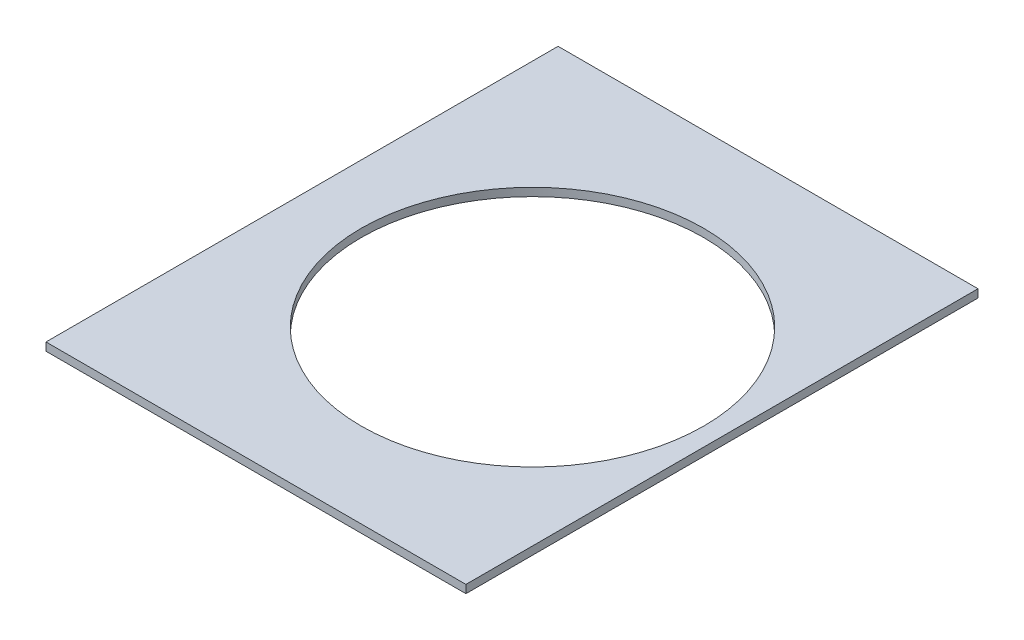
SolidWorks part; units mm, degrees
ref_plane "Front Plane" through (0, 0, 0) normal (0, 0, 1) x (1, 0, 0)
ref_plane "Top Plane" through (0, 0, 0) normal (0, 1, 0) x (1, 0, 0)
ref_plane "Right Plane" through (0, 0, 0) normal (1, 0, 0) x (0, 0, -1)
sketch "Sketch3" plane through (0, 0, 0) normal (0, 1, 0) x (1, 0, 0)
  line L0 (0, 0) -> (0, 63.5)
  line L1 (0, 63.5) -> (52.07, 63.5)
  line L2 (52.07, 63.5) -> (52.07, 0)
  line L3 (52.07, 0) -> (0, 0)
  line L4 (28.575, 63.5) -> (28.575, 0)
  line L7 (24.257, 63.5) -> (24.257, 52.5466)
  line L8 (32.893, 63.5) -> (32.893, 52.5466)
  line L9 (24.257, 0) -> (24.257, 10.9534)
  line L10 (32.893, 0) -> (32.893, 10.9534)
  circle A0 centre (28.575, 31.75) radius 18.669
  arc A2 (24.257, 52.5466) -> (24.257, 10.9534) centre (28.575, 31.75) ccw
  arc A3 (32.893, 10.9534) -> (32.893, 52.5466) centre (28.575, 31.75) ccw
  circle A4 centre (28.575, 31.75) radius 21.2402
extrude "Boss-Extrude1" add sketch "Sketch3" along normal blind 1.0008 contours A2 L7 L1 L0 L3 L9 | A3 L10 L3 L2 L1 L8 | A4 L4 L3 L10 | A4 L9 L3 L4 | A4 L8 L1 L4 | A4 L4 L1 L7
